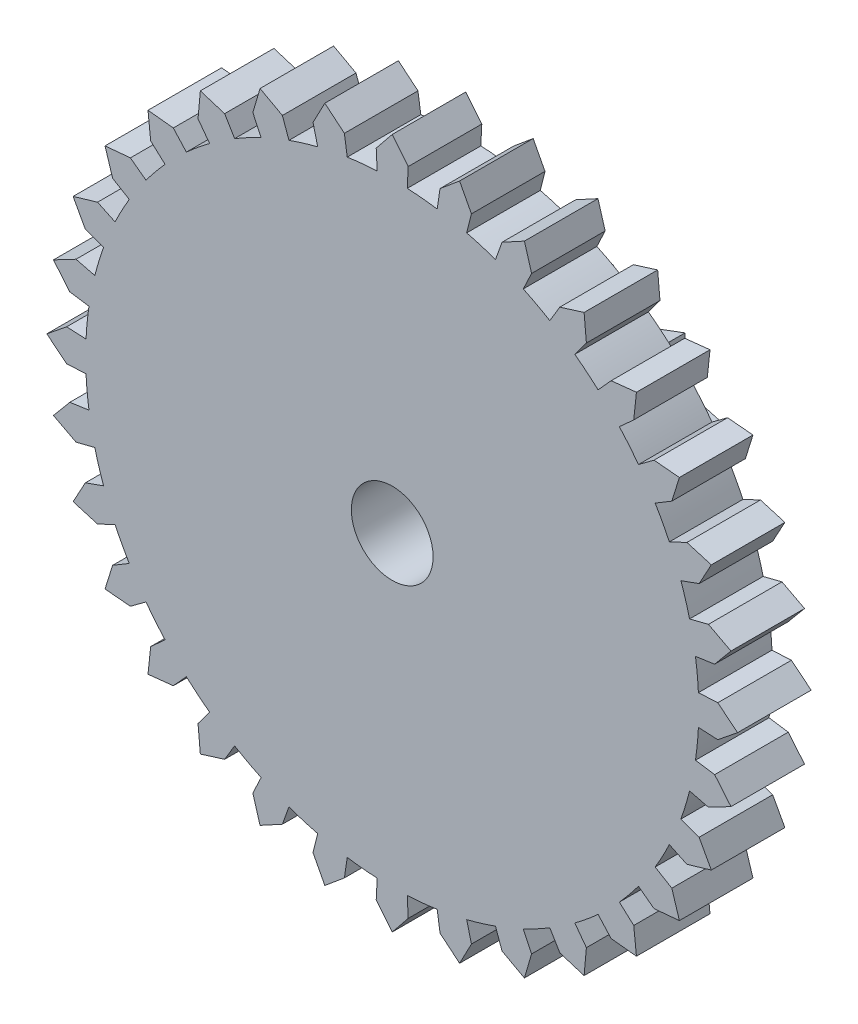
SolidWorks part; units mm, degrees
ref_plane "Front Plane" through (0, 0, 0) normal (0, 0, 1) x (1, 0, 0)
ref_plane "Top Plane" through (0, 0, 0) normal (0, 1, 0) x (1, 0, 0)
ref_plane "Right Plane" through (0, 0, 0) normal (1, 0, 0) x (0, 0, -1)
sketch "Sketch1" plane through (0, 0, 0) normal (0, 0, 1) x (1, 0, 0)
  line L0 (1.9378, 7.736) -> (1.6485, 8.2876)
  line L1 (0.3913, 7.9654) -> (0, 8.45)
  line L2 (-0.368, 7.491) -> (-0.3913, 7.9654)
  line L3 (-0.3913, 7.9654) -> (0, 8.45)
  line L4 (0.368, 7.491) -> (0.3913, 7.9654)
  line L5 (1.1005, 7.4188) -> (1.1702, 7.8887)
  line L6 (1.1702, 7.8887) -> (1.6485, 8.2876)
  line L7 (1.8224, 7.2752) -> (1.9378, 7.736)
  line L8 (3.4098, 7.2093) -> (3.2337, 7.8068)
  line L9 (2.5267, 7.0616) -> (2.6867, 7.5088)
  line L10 (2.6867, 7.5088) -> (3.2337, 7.8068)
  line L11 (3.2067, 6.7799) -> (3.4098, 7.2093)
  line L12 (4.7507, 6.4056) -> (4.6946, 7.0259)
  line L13 (3.8558, 6.433) -> (4.1, 6.8404)
  line L14 (4.1, 6.8404) -> (4.6946, 7.0259)
  line L15 (4.4677, 6.0241) -> (4.7507, 6.4056)
  line L16 (5.9091, 5.3557) -> (5.9751, 5.9751)
  line L17 (5.0367, 5.5571) -> (5.3557, 5.9091)
  line L18 (5.3557, 5.9091) -> (5.9751, 5.9751)
  line L19 (5.5571, 5.0367) -> (5.9091, 5.3557)
  line L20 (6.8404, 4.1) -> (7.0259, 4.6946)
  line L21 (6.0241, 4.4677) -> (6.4056, 4.7507)
  line L22 (6.4056, 4.7507) -> (7.0259, 4.6946)
  line L23 (6.433, 3.8558) -> (6.8404, 4.1)
  line L24 (7.5088, 2.6867) -> (7.8068, 3.2337)
  line L25 (6.7799, 3.2067) -> (7.2093, 3.4098)
  line L26 (7.2093, 3.4098) -> (7.8068, 3.2337)
  line L27 (7.0616, 2.5267) -> (7.5088, 2.6867)
  line L28 (7.8887, 1.1702) -> (8.2876, 1.6485)
  line L29 (7.2752, 1.8224) -> (7.736, 1.9378)
  line L30 (7.736, 1.9378) -> (8.2876, 1.6485)
  line L31 (7.4188, 1.1005) -> (7.8887, 1.1702)
  line L32 (7.9654, -0.3913) -> (8.45, 0)
  line L33 (7.491, 0.368) -> (7.9654, 0.3913)
  line L34 (7.9654, 0.3913) -> (8.45, 0)
  line L35 (7.491, -0.368) -> (7.9654, -0.3913)
  line L36 (7.736, -1.9378) -> (8.2876, -1.6485)
  line L37 (7.4188, -1.1005) -> (7.8887, -1.1702)
  line L38 (7.8887, -1.1702) -> (8.2876, -1.6485)
  line L39 (7.2752, -1.8224) -> (7.736, -1.9378)
  line L40 (7.2093, -3.4098) -> (7.8068, -3.2337)
  line L41 (7.0616, -2.5267) -> (7.5088, -2.6867)
  line L42 (7.5088, -2.6867) -> (7.8068, -3.2337)
  line L43 (6.7799, -3.2067) -> (7.2093, -3.4098)
  line L44 (6.4056, -4.7507) -> (7.0259, -4.6946)
  line L45 (6.433, -3.8558) -> (6.8404, -4.1)
  line L46 (6.8404, -4.1) -> (7.0259, -4.6946)
  line L47 (6.0241, -4.4677) -> (6.4056, -4.7507)
  line L48 (5.3557, -5.9091) -> (5.9751, -5.9751)
  line L49 (5.5571, -5.0367) -> (5.9091, -5.3557)
  line L50 (5.9091, -5.3557) -> (5.9751, -5.9751)
  line L51 (5.0367, -5.5571) -> (5.3557, -5.9091)
  line L52 (4.1, -6.8404) -> (4.6946, -7.0259)
  line L53 (4.4677, -6.0241) -> (4.7507, -6.4056)
  line L54 (4.7507, -6.4056) -> (4.6946, -7.0259)
  line L55 (3.8558, -6.433) -> (4.1, -6.8404)
  line L56 (2.6867, -7.5088) -> (3.2337, -7.8068)
  line L57 (3.2067, -6.7799) -> (3.4098, -7.2093)
  line L58 (3.4098, -7.2093) -> (3.2337, -7.8068)
  line L59 (2.5267, -7.0616) -> (2.6867, -7.5088)
  line L60 (1.1702, -7.8887) -> (1.6485, -8.2876)
  line L61 (1.8224, -7.2752) -> (1.9378, -7.736)
  line L62 (1.9378, -7.736) -> (1.6485, -8.2876)
  line L63 (1.1005, -7.4188) -> (1.1702, -7.8887)
  line L64 (-0.3913, -7.9654) -> (0, -8.45)
  line L65 (0.368, -7.491) -> (0.3913, -7.9654)
  line L66 (0.3913, -7.9654) -> (0, -8.45)
  line L67 (-0.368, -7.491) -> (-0.3913, -7.9654)
  line L68 (-1.9378, -7.736) -> (-1.6485, -8.2876)
  line L69 (-1.1005, -7.4188) -> (-1.1702, -7.8887)
  line L70 (-1.1702, -7.8887) -> (-1.6485, -8.2876)
  line L71 (-1.8224, -7.2752) -> (-1.9378, -7.736)
  line L72 (-3.4098, -7.2093) -> (-3.2337, -7.8068)
  line L73 (-2.5267, -7.0616) -> (-2.6867, -7.5088)
  line L74 (-2.6867, -7.5088) -> (-3.2337, -7.8068)
  line L75 (-3.2067, -6.7799) -> (-3.4098, -7.2093)
  line L76 (-4.7507, -6.4056) -> (-4.6946, -7.0259)
  line L77 (-3.8558, -6.433) -> (-4.1, -6.8404)
  line L78 (-4.1, -6.8404) -> (-4.6946, -7.0259)
  line L79 (-4.4677, -6.0241) -> (-4.7507, -6.4056)
  line L80 (-5.9091, -5.3557) -> (-5.9751, -5.9751)
  line L81 (-5.0367, -5.5571) -> (-5.3557, -5.9091)
  line L82 (-5.3557, -5.9091) -> (-5.9751, -5.9751)
  line L83 (-5.5571, -5.0367) -> (-5.9091, -5.3557)
  line L84 (-6.8404, -4.1) -> (-7.0259, -4.6946)
  line L85 (-6.0241, -4.4677) -> (-6.4056, -4.7507)
  line L86 (-6.4056, -4.7507) -> (-7.0259, -4.6946)
  line L87 (-6.433, -3.8558) -> (-6.8404, -4.1)
  line L88 (-7.5088, -2.6867) -> (-7.8068, -3.2337)
  line L89 (-6.7799, -3.2067) -> (-7.2093, -3.4098)
  line L90 (-7.2093, -3.4098) -> (-7.8068, -3.2337)
  line L91 (-7.0616, -2.5267) -> (-7.5088, -2.6867)
  line L92 (-7.8887, -1.1702) -> (-8.2876, -1.6485)
  line L93 (-7.2752, -1.8224) -> (-7.736, -1.9378)
  line L94 (-7.736, -1.9378) -> (-8.2876, -1.6485)
  line L95 (-7.4188, -1.1005) -> (-7.8887, -1.1702)
  line L96 (-7.9654, 0.3913) -> (-8.45, 0)
  line L97 (-7.491, -0.368) -> (-7.9654, -0.3913)
  line L98 (-7.9654, -0.3913) -> (-8.45, 0)
  line L99 (-7.491, 0.368) -> (-7.9654, 0.3913)
  line L100 (-7.736, 1.9378) -> (-8.2876, 1.6485)
  line L101 (-7.4188, 1.1005) -> (-7.8887, 1.1702)
  line L102 (-7.8887, 1.1702) -> (-8.2876, 1.6485)
  line L103 (-7.2752, 1.8224) -> (-7.736, 1.9378)
  line L104 (-7.2093, 3.4098) -> (-7.8068, 3.2337)
  line L105 (-7.0616, 2.5267) -> (-7.5088, 2.6867)
  line L106 (-7.5088, 2.6867) -> (-7.8068, 3.2337)
  line L107 (-6.7799, 3.2067) -> (-7.2093, 3.4098)
  line L108 (-6.4056, 4.7507) -> (-7.0259, 4.6946)
  line L109 (-6.433, 3.8558) -> (-6.8404, 4.1)
  line L110 (-6.8404, 4.1) -> (-7.0259, 4.6946)
  line L111 (-6.0241, 4.4677) -> (-6.4056, 4.7507)
  line L112 (-5.3557, 5.9091) -> (-5.9751, 5.9751)
  line L113 (-5.5571, 5.0367) -> (-5.9091, 5.3557)
  line L114 (-5.9091, 5.3557) -> (-5.9751, 5.9751)
  line L115 (-5.0367, 5.5571) -> (-5.3557, 5.9091)
  line L116 (-4.1, 6.8404) -> (-4.6946, 7.0259)
  line L117 (-4.4677, 6.0241) -> (-4.7507, 6.4056)
  line L118 (-4.7507, 6.4056) -> (-4.6946, 7.0259)
  line L119 (-3.8558, 6.433) -> (-4.1, 6.8404)
  line L120 (-2.6867, 7.5088) -> (-3.2337, 7.8068)
  line L121 (-3.2067, 6.7799) -> (-3.4098, 7.2093)
  line L122 (-3.4098, 7.2093) -> (-3.2337, 7.8068)
  line L123 (-2.5267, 7.0616) -> (-2.6867, 7.5088)
  line L124 (-1.1702, 7.8887) -> (-1.6485, 8.2876)
  line L125 (-1.8224, 7.2752) -> (-1.9378, 7.736)
  line L126 (-1.9378, 7.736) -> (-1.6485, 8.2876)
  line L127 (-1.1005, 7.4188) -> (-1.1702, 7.8887)
  arc A0 (0.368, 7.491) -> (0.7351, 7.4639) centre (0, 0) cw
  arc A1 (-0.368, 7.491) -> (-0.7351, 7.4639) centre (0, 0) ccw
  arc A2 (1.8224, 7.2752) -> (2.1771, 7.1771) centre (0, 0) cw
  arc A3 (1.1005, 7.4188) -> (0.7351, 7.4639) centre (0, 0) ccw
  arc A4 (3.2067, 6.7799) -> (3.5355, 6.6144) centre (0, 0) cw
  arc A5 (2.5267, 7.0616) -> (2.1771, 7.1771) centre (0, 0) ccw
  arc A6 (4.4677, 6.0241) -> (4.7579, 5.7976) centre (0, 0) cw
  arc A7 (3.8558, 6.433) -> (3.5355, 6.6144) centre (0, 0) ccw
  arc A8 (5.5571, 5.0367) -> (5.7976, 4.7579) centre (0, 0) cw
  arc A9 (5.0367, 5.5571) -> (4.7579, 5.7976) centre (0, 0) ccw
  arc A10 (6.433, 3.8558) -> (6.6144, 3.5355) centre (0, 0) cw
  arc A11 (6.0241, 4.4677) -> (5.7976, 4.7579) centre (0, 0) ccw
  arc A12 (7.0616, 2.5267) -> (7.1771, 2.1771) centre (0, 0) cw
  arc A13 (6.7799, 3.2067) -> (6.6144, 3.5355) centre (0, 0) ccw
  arc A14 (7.4188, 1.1005) -> (7.4639, 0.7351) centre (0, 0) cw
  arc A15 (7.2752, 1.8224) -> (7.1771, 2.1771) centre (0, 0) ccw
  arc A16 (7.491, -0.368) -> (7.4639, -0.7351) centre (0, 0) cw
  arc A17 (7.491, 0.368) -> (7.4639, 0.7351) centre (0, 0) ccw
  arc A18 (7.2752, -1.8224) -> (7.1771, -2.1771) centre (0, 0) cw
  arc A19 (7.4188, -1.1005) -> (7.4639, -0.7351) centre (0, 0) ccw
  arc A20 (6.7799, -3.2067) -> (6.6144, -3.5355) centre (0, 0) cw
  arc A21 (7.0616, -2.5267) -> (7.1771, -2.1771) centre (0, 0) ccw
  arc A22 (6.0241, -4.4677) -> (5.7976, -4.7579) centre (0, 0) cw
  arc A23 (6.433, -3.8558) -> (6.6144, -3.5355) centre (0, 0) ccw
  arc A24 (5.0367, -5.5571) -> (4.7579, -5.7976) centre (0, 0) cw
  arc A25 (5.5571, -5.0367) -> (5.7976, -4.7579) centre (0, 0) ccw
  arc A26 (3.8558, -6.433) -> (3.5355, -6.6144) centre (0, 0) cw
  arc A27 (4.4677, -6.0241) -> (4.7579, -5.7976) centre (0, 0) ccw
  arc A28 (2.5267, -7.0616) -> (2.1771, -7.1771) centre (0, 0) cw
  arc A29 (3.2067, -6.7799) -> (3.5355, -6.6144) centre (0, 0) ccw
  arc A30 (1.1005, -7.4188) -> (0.7351, -7.4639) centre (0, 0) cw
  arc A31 (1.8224, -7.2752) -> (2.1771, -7.1771) centre (0, 0) ccw
  arc A32 (-0.368, -7.491) -> (-0.7351, -7.4639) centre (0, 0) cw
  arc A33 (0.368, -7.491) -> (0.7351, -7.4639) centre (0, 0) ccw
  arc A34 (-1.8224, -7.2752) -> (-2.1771, -7.1771) centre (0, 0) cw
  arc A35 (-1.1005, -7.4188) -> (-0.7351, -7.4639) centre (0, 0) ccw
  arc A36 (-3.2067, -6.7799) -> (-3.5355, -6.6144) centre (0, 0) cw
  arc A37 (-2.5267, -7.0616) -> (-2.1771, -7.1771) centre (0, 0) ccw
  arc A38 (-4.4677, -6.0241) -> (-4.7579, -5.7976) centre (0, 0) cw
  arc A39 (-3.8558, -6.433) -> (-3.5355, -6.6144) centre (0, 0) ccw
  arc A40 (-5.5571, -5.0367) -> (-5.7976, -4.7579) centre (0, 0) cw
  arc A41 (-5.0367, -5.5571) -> (-4.7579, -5.7976) centre (0, 0) ccw
  arc A42 (-6.433, -3.8558) -> (-6.6144, -3.5355) centre (0, 0) cw
  arc A43 (-6.0241, -4.4677) -> (-5.7976, -4.7579) centre (0, 0) ccw
  arc A44 (-7.0616, -2.5267) -> (-7.1771, -2.1771) centre (0, 0) cw
  arc A45 (-6.7799, -3.2067) -> (-6.6144, -3.5355) centre (0, 0) ccw
  arc A46 (-7.4188, -1.1005) -> (-7.4639, -0.7351) centre (0, 0) cw
  arc A47 (-7.2752, -1.8224) -> (-7.1771, -2.1771) centre (0, 0) ccw
  arc A48 (-7.491, 0.368) -> (-7.4639, 0.7351) centre (0, 0) cw
  arc A49 (-7.491, -0.368) -> (-7.4639, -0.7351) centre (0, 0) ccw
  arc A50 (-7.2752, 1.8224) -> (-7.1771, 2.1771) centre (0, 0) cw
  arc A51 (-7.4188, 1.1005) -> (-7.4639, 0.7351) centre (0, 0) ccw
  arc A52 (-6.7799, 3.2067) -> (-6.6144, 3.5355) centre (0, 0) cw
  arc A53 (-7.0616, 2.5267) -> (-7.1771, 2.1771) centre (0, 0) ccw
  arc A54 (-6.0241, 4.4677) -> (-5.7976, 4.7579) centre (0, 0) cw
  arc A55 (-6.433, 3.8558) -> (-6.6144, 3.5355) centre (0, 0) ccw
  arc A56 (-5.0367, 5.5571) -> (-4.7579, 5.7976) centre (0, 0) cw
  arc A57 (-5.5571, 5.0367) -> (-5.7976, 4.7579) centre (0, 0) ccw
  arc A58 (-3.8558, 6.433) -> (-3.5355, 6.6144) centre (0, 0) cw
  arc A59 (-4.4677, 6.0241) -> (-4.7579, 5.7976) centre (0, 0) ccw
  arc A60 (-2.5267, 7.0616) -> (-2.1771, 7.1771) centre (0, 0) cw
  arc A61 (-3.2067, 6.7799) -> (-3.5355, 6.6144) centre (0, 0) ccw
  arc A62 (-1.1005, 7.4188) -> (-0.7351, 7.4639) centre (0, 0) cw
  arc A63 (-1.8224, 7.2752) -> (-2.1771, 7.1771) centre (0, 0) ccw
  circle A64 centre (0, 0) radius 1
  point P228 (0, 0)
  dimension "D1" = 32
  dimension "D2" = 15
  dimension "D3" = 2
extrude "Boss-Extrude1" add sketch "Sketch1" along normal blind 1.8
sketch "Sketch2" plane through (0, 0, 0) normal (0, 0, 1) x (1, 0, 0)
  line L0 (1.7349, 1.7804) -> (1.7634, 2.4271)
  line L1 (0.3571, 2.4601) -> (0, 3)
  line L2 (-0.2801, 1.9298) -> (-0.3571, 2.4601)
  line L3 (-0.3571, 2.4601) -> (0, 3)
  line L4 (0.2801, 1.9298) -> (0.3571, 2.4601)
  line L5 (0.9077, 1.7259) -> (1.1571, 2.2001)
  line L6 (1.1571, 2.2001) -> (1.7634, 2.4271)
  line L7 (1.3609, 1.3966) -> (1.7349, 1.7804)
  line L8 (2.45, 0.4206) -> (2.8532, 0.9271)
  line L9 (1.7488, 0.8627) -> (2.2294, 1.0998)
  line L10 (2.2294, 1.0998) -> (2.8532, 0.9271)
  line L11 (1.9219, 0.33) -> (2.45, 0.4206)
  line L12 (2.2294, -1.0998) -> (2.8532, -0.9271)
  line L13 (1.9219, -0.33) -> (2.45, -0.4206)
  line L14 (2.45, -0.4206) -> (2.8532, -0.9271)
  line L15 (1.7488, -0.8627) -> (2.2294, -1.0998)
  line L16 (1.1571, -2.2001) -> (1.7634, -2.4271)
  line L17 (1.3609, -1.3966) -> (1.7349, -1.7804)
  line L18 (1.7349, -1.7804) -> (1.7634, -2.4271)
  line L19 (0.9077, -1.7259) -> (1.1571, -2.2001)
  line L20 (-0.3571, -2.4601) -> (0, -3)
  line L21 (0.2801, -1.9298) -> (0.3571, -2.4601)
  line L22 (0.3571, -2.4601) -> (0, -3)
  line L23 (-0.2801, -1.9298) -> (-0.3571, -2.4601)
  line L24 (-1.7349, -1.7804) -> (-1.7634, -2.4271)
  line L25 (-0.9077, -1.7259) -> (-1.1571, -2.2001)
  line L26 (-1.1571, -2.2001) -> (-1.7634, -2.4271)
  line L27 (-1.3609, -1.3966) -> (-1.7349, -1.7804)
  line L28 (-2.45, -0.4206) -> (-2.8532, -0.9271)
  line L29 (-1.7488, -0.8627) -> (-2.2294, -1.0998)
  line L30 (-2.2294, -1.0998) -> (-2.8532, -0.9271)
  line L31 (-1.9219, -0.33) -> (-2.45, -0.4206)
  line L32 (-2.2294, 1.0998) -> (-2.8532, 0.9271)
  line L33 (-1.9219, 0.33) -> (-2.45, 0.4206)
  line L34 (-2.45, 0.4206) -> (-2.8532, 0.9271)
  line L35 (-1.7488, 0.8627) -> (-2.2294, 1.0998)
  line L36 (-1.1571, 2.2001) -> (-1.7634, 2.4271)
  line L37 (-1.3609, 1.3966) -> (-1.7349, 1.7804)
  line L38 (-1.7349, 1.7804) -> (-1.7634, 2.4271)
  line L39 (-0.9077, 1.7259) -> (-1.1571, 2.2001)
  arc A0 (0.2801, 1.9298) -> (0.6026, 1.8546) centre (0, 0) cw
  arc A1 (-0.2801, 1.9298) -> (-0.6026, 1.8546) centre (0, 0) ccw
  arc A2 (1.3609, 1.3966) -> (1.5776, 1.1462) centre (0, 0) cw
  arc A3 (0.9077, 1.7259) -> (0.6026, 1.8546) centre (0, 0) ccw
  arc A4 (1.9219, 0.33) -> (1.95, 0) centre (0, 0) cw
  arc A5 (1.7488, 0.8627) -> (1.5776, 1.1462) centre (0, 0) ccw
  arc A6 (1.7488, -0.8627) -> (1.5776, -1.1462) centre (0, 0) cw
  arc A7 (1.9219, -0.33) -> (1.95, 0) centre (0, 0) ccw
  arc A8 (0.9077, -1.7259) -> (0.6026, -1.8546) centre (0, 0) cw
  arc A9 (1.3609, -1.3966) -> (1.5776, -1.1462) centre (0, 0) ccw
  arc A10 (-0.2801, -1.9298) -> (-0.6026, -1.8546) centre (0, 0) cw
  arc A11 (0.2801, -1.9298) -> (0.6026, -1.8546) centre (0, 0) ccw
  arc A12 (-1.3609, -1.3966) -> (-1.5776, -1.1462) centre (0, 0) cw
  arc A13 (-0.9077, -1.7259) -> (-0.6026, -1.8546) centre (0, 0) ccw
  arc A14 (-1.9219, -0.33) -> (-1.95, 0) centre (0, 0) cw
  arc A15 (-1.7488, -0.8627) -> (-1.5776, -1.1462) centre (0, 0) ccw
  arc A16 (-1.7488, 0.8627) -> (-1.5776, 1.1462) centre (0, 0) cw
  arc A17 (-1.9219, 0.33) -> (-1.95, 0) centre (0, 0) ccw
  arc A18 (-0.9077, 1.7259) -> (-0.6026, 1.8546) centre (0, 0) cw
  arc A19 (-1.3609, 1.3966) -> (-1.5776, 1.1462) centre (0, 0) ccw
  circle A20 centre (0, 0) radius 1 construction
  circle A21 centre (0, 0) radius 1
  point P75 (0, 0)
  dimension "D1" = 3.9
  dimension "D2" = 10
extrude "Boss-Extrude2" add sketch "Sketch2" against normal blind 3.6
